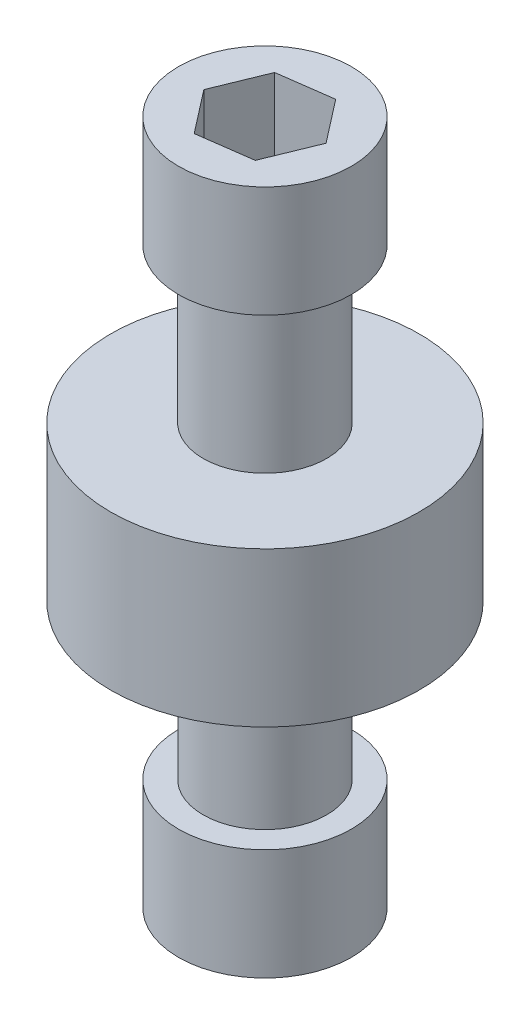
SolidWorks part; units mm, degrees
ref_plane "Front Plane" through (0, 0, 0) normal (0, 0, 1) x (1, 0, 0)
ref_plane "Top Plane" through (0, 0, 0) normal (0, 1, 0) x (1, 0, 0)
ref_plane "Right Plane" through (0, 0, 0) normal (1, 0, 0) x (0, 0, -1)
sketch "Sketch1" plane through (0, 0, 0) normal (0, 1, 0) x (1, 0, 0)
  circle A0 centre (0, 0) radius 6.35
  dimension "D1" = 12.7
extrude "Boss-Extrude1" add sketch "Sketch1" along normal blind 6.35
sketch "Sketch2" plane through (0, 6.35, 0) normal (0, 1, 0) x (1, 0, 0)
  circle A0 centre (0, 0) radius 2.54
extrude "Boss-Extrude2" add sketch "Sketch2" along normal blind 6.35
sketch "Sketch3" plane through (0, 12.7, 0) normal (0, 1, 0) x (1, 0, 0)
  circle A0 centre (0, 0) radius 3.556
extrude "Boss-Extrude3" add sketch "Sketch3" along normal blind 4.572
sketch "Sketch4" plane through (0, 17.272, 0) normal (0, 1, 0) x (1, 0, 0)
  line L1 (2.2126, 0.302) -> (0.8447, 2.0671)
  line L2 (0.8447, 2.0671) -> (-1.3678, 1.7651)
  line L3 (-1.3678, 1.7651) -> (-2.2126, -0.302)
  line L4 (-2.2126, -0.302) -> (-0.8447, -2.0671)
  line L5 (-0.8447, -2.0671) -> (1.3678, -1.7651)
  line L6 (1.3678, -1.7651) -> (2.2126, 0.302)
  circle A0 centre (0, 0) radius 1.9339 construction
extrude "Cut-Extrude1" cut sketch "Sketch4" against normal blind 3.556
ref_plane "Plane1" through (0, 3.175, 0) normal (0, 1, 0) x (1, 0, 0)
mirror "Mirror1" about plane through (0, 3.175, 0) normal (0, 1, 0) of "Cut-Extrude1", "Boss-Extrude3", "Boss-Extrude2"
